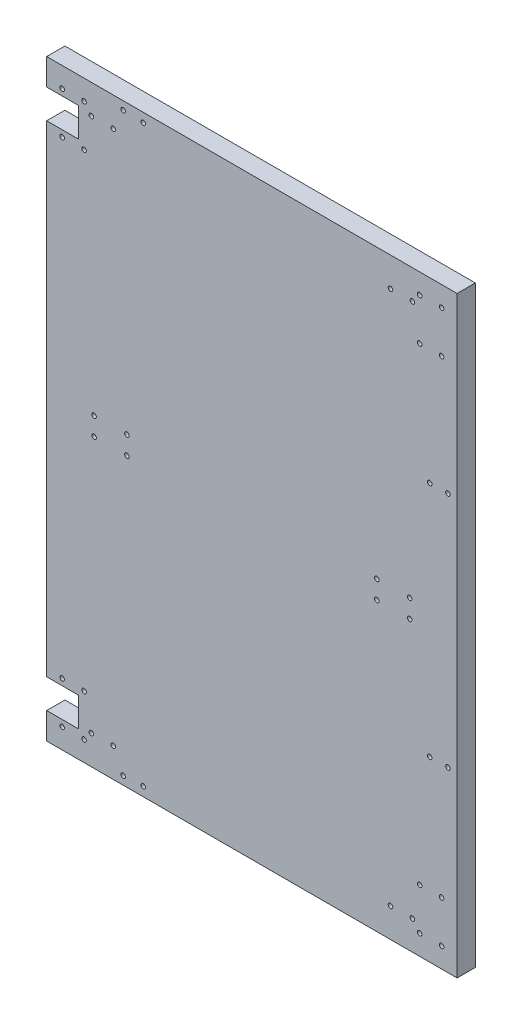
SolidWorks part; units mm, degrees
ref_plane "前视基准面" through (0, 0, 0) normal (0, 0, 1) x (1, 0, 0)
ref_plane "上视基准面" through (0, 0, 0) normal (0, 1, 0) x (1, 0, 0)
ref_plane "右视基准面" through (0, 0, 0) normal (1, 0, 0) x (0, 0, -1)
sketch "草图1" plane through (0, 0, 0) normal (0, 0, 1) x (1, 0, 0)
  line L1 (-225, -325) -> (225, -325)
  line L2 (-225, -325) -> (-225, 325)
  line L3 (-225, 325) -> (225, 325)
  line L4 (225, -325) -> (225, 325)
  line L5 (-225, -325) -> (225, 325) construction
  line L6 (-225, 325) -> (225, -325) construction
  point P0 (0, 0)
  dimension "D1" = 650
  dimension "D2" = 450
extrude "凸台-拉伸1" add sketch "草图1" along normal blind 20
sketch "草图2" plane through (0, 0, 20) normal (0, 0, 1) x (1, 0, 0)
  line L0 (0, -325) -> (0, -319) construction
  line L1 (-225, -325) -> (225, -325) construction
  line L2 (225, -325) -> (225, 325) construction
  line L3 (0, -319) -> (-100, -319) construction
  circle A0 centre (137, 10) radius 2.5
  circle A1 centre (173, 10) radius 2.5
  circle A2 centre (173, -10) radius 2.5
  circle A3 centre (137, -10) radius 2.5
  circle A4 centre (-100, -319) radius 2
  dimension "D3" = 100
  dimension "D4" = 4
  dimension "D1" = 52
  dimension "D2" = 6
extrude "切除-拉伸1" cut sketch "草图2" against normal through all contours A0 | A1 | A3 | A2
sketch "草图3" plane through (0, 0, 20) normal (0, 0, 1) x (1, 0, 0)
  line L1 (225, -325) -> (225, 325) construction
  circle A1 centre (152, -293) radius 2.5
  circle A2 centre (176, -293) radius 2.5
  dimension "D1" = 49
  dimension "D2" = 24
extrude "切除-拉伸2" cut sketch "草图3" against normal through all contours A1 | A2
sketch "草图4" plane through (0, 0, 20) normal (0, 0, 1) x (1, 0, 0)
  line L0 (0, -325) -> (0, -319) construction
  line L1 (-225, -325) -> (225, -325) construction
  line L2 (225, -325) -> (225, 325) construction
  line L3 (0, -319) -> (-100, -319) construction
  circle A0 centre (184, -303) radius 2.5
  circle A1 centre (208, -303) radius 2.5
  circle A2 centre (184, -257) radius 2.5
  circle A3 centre (208, -257) radius 2.5
  circle A4 centre (-100, -319) radius 2
  dimension "D4" = 100
  dimension "D5" = 4
  dimension "D1" = 6
  dimension "D2" = 17
  dimension "D3" = 24
extrude "切除-拉伸3" cut sketch "草图4" against normal through all contours A2 | A3 | A0 | A1
sketch "草图5" plane through (0, 0, 20) normal (0, 0, 1) x (1, 0, 0)
  line L1 (225, -325) -> (225, 325) construction
  line L2 (0, 0) -> (259.3301, 0)
  circle A0 centre (195, -130) radius 2.5
  circle A1 centre (215, -130) radius 2.5
  circle A2 centre (215, 130) radius 2.5
  circle A3 centre (195, 130) radius 2.5
  dimension "D1" = 10
  dimension "D2" = 20
extrude "切除-拉伸4" cut sketch "草图5" against normal through all contours A0 | A1 | A3 | A2
mirror "镜向5" about plane through (0, 0, 0) normal (0, 1, 0) of "切除-拉伸3", "切除-拉伸2"
mirror "镜向6" about plane through (0, 0, 0) normal (1, 0, 0) of "镜向5", "切除-拉伸1", "切除-拉伸3", "切除-拉伸2"
sketch "草图6" plane through (0, 0, 20) normal (0, 0, 1) x (1, 0, 0)
  line L0 (-225, -264) -> (-190, -264)
  line L2 (-225, 325) -> (-225, -325) construction
  line L3 (-190, -264) -> (-190, -296)
  line L4 (-190, -296) -> (-225, -296)
  circle A0 centre (-208, -257) radius 2.5 construction
  dimension "D2" = 7
  dimension "D1" = 32
  dimension "D3" = 35
extrude "切除-拉伸5" cut sketch "草图6" against normal through all and the other way through all flip side to cut
mirror "镜向7" about plane through (0, 0, 0) normal (0, 1, 0) of "切除-拉伸5"
sketch "草图7" plane through (0, 0, 20) normal (0, 0, 1) x (1, 0, 0)
  line L0 (-225, -325) -> (225, -325) construction
  circle A0 centre (-119.1211, -315) radius 2.5
  dimension "D2" = 5
  dimension "D1" = 10
extrude "切除-拉伸6" cut sketch "草图7" against normal through all
mirror "镜向8" about plane through (0, 0, 0) normal (0, 1, 0) of "切除-拉伸6"
sketch "草图9" plane through (0, 0, 20) normal (0, 0, 1) x (1, 0, 0)
  circle A0 centre (-141.1121, -315.9453) radius 2.5
extrude "切除-拉伸7" cut sketch "草图9" against normal through all
mirror "镜向9" about plane through (0, 0, 0) normal (0, 1, 0) of "切除-拉伸7"
